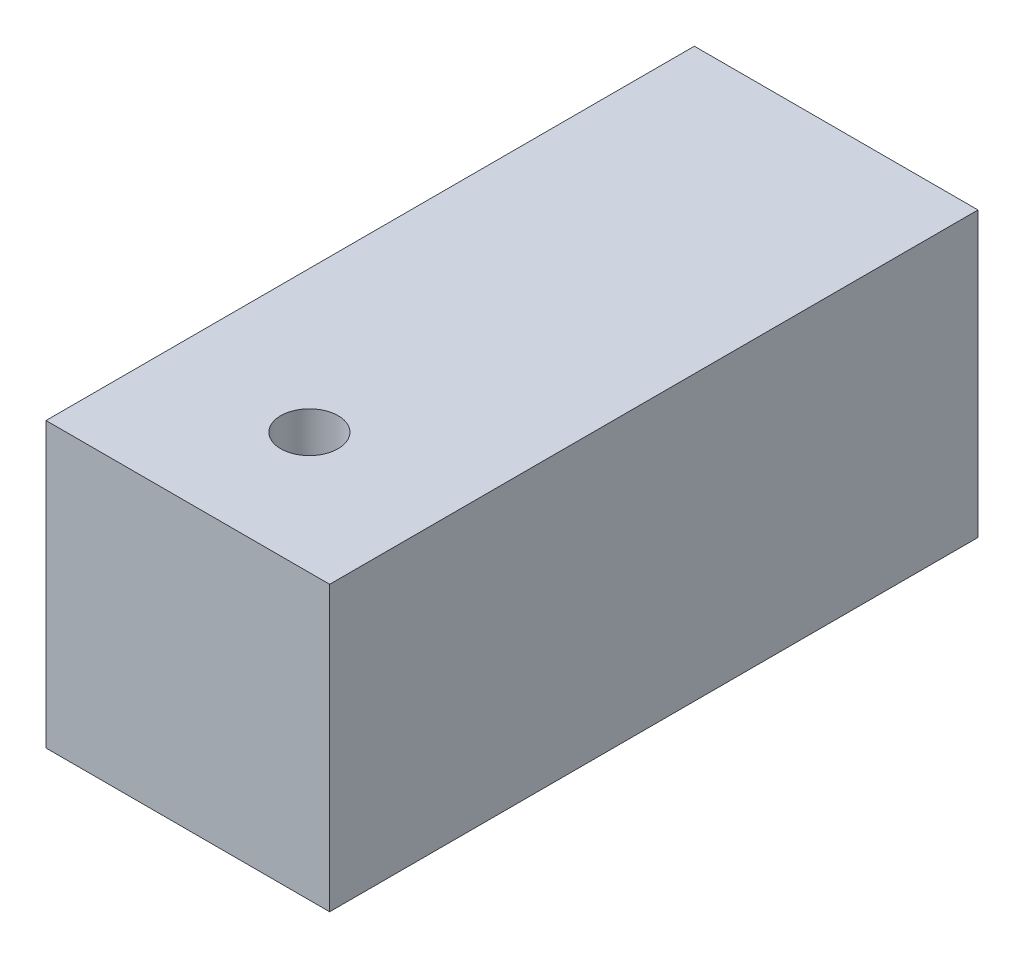
SolidWorks part; units mm, degrees
material "AISI 304"
ref_plane "Front Plane" through (0, 0, 0) normal (0, 0, 1) x (1, 0, 0)
ref_plane "Top Plane" through (0, 0, 0) normal (0, 1, 0) x (1, 0, 0)
ref_plane "Right Plane" through (0, 0, 0) normal (1, 0, 0) x (0, 0, -1)
sketch "Sketch1" plane through (0, 0, 0) normal (0, 0, 1) x (1, 0, 0)
  line L1 (-11.1125, 11.1125) -> (11.1125, 11.1125)
  line L2 (-11.1125, 11.1125) -> (-11.1125, -11.1125)
  line L3 (-11.1125, -11.1125) -> (11.1125, -11.1125)
  line L4 (11.1125, 11.1125) -> (11.1125, -11.1125)
  line L5 (-11.1125, 11.1125) -> (11.1125, -11.1125) construction
  line L6 (-11.1125, -11.1125) -> (11.1125, 11.1125) construction
  point P0 (0, 0)
  dimension "D1" = 22.225
  dimension "D2" = 22.225
extrude "Boss-Extrude1" add sketch "Sketch1" along normal blind 50.8
sketch "Sketch2" plane through (0, -11.1125, 0) normal (0, -1, 0) x (1, 0, 0)
  line L3 (-0.7938, 47.625) -> (0.7938, 47.625)
  line L4 (-3.9688, 44.45) -> (-3.9688, 38.1)
  line L5 (-0.7938, 34.925) -> (0.7938, 34.925)
  line L6 (3.9688, 44.45) -> (3.9688, 38.1)
  line L7 (-3.9688, 47.625) -> (3.9688, 34.925) construction
  line L8 (-3.9688, 34.925) -> (3.9688, 47.625) construction
  line L10 (-11.1125, 50.8) -> (11.1125, 50.8) construction
  circle A2 centre (0, 41.275) radius 6.35
  arc A3 (-3.9688, 38.1) -> (-0.7938, 34.925) centre (-0.7938, 38.1) ccw
  arc A4 (0.7938, 34.925) -> (3.9688, 38.1) centre (0.7938, 38.1) ccw
  arc A5 (3.9688, 44.45) -> (0.7938, 47.625) centre (0.7938, 44.45) ccw
  arc A6 (-0.7938, 47.625) -> (-3.9688, 44.45) centre (-0.7938, 44.45) ccw
  dimension "D2" = 12.7
  dimension "D1" = 3.175
  dimension "D3" = 7.9375
  dimension "D4" = 9.525
extrude "Cut-Extrude1" cut sketch "Sketch2" against normal blind 12.7 contours L4 A3 L5 A4 L6 A5 L3 A6
hole_wizard "#8 Clearance Hole1" positions "Sketch3" profile "Sketch4" hole size "#8" standard "ANSI Inch" end condition through all
sketch "Sketch3" plane through (0, 1.5875, 0) normal (0, -1, 0) x (-1, 0, 0)
  line L0 (-3.9688, -41.275) -> (3.9688, -41.275)
  line L1 (-3.9688, -44.45) -> (-3.9688, -38.1) construction
  line L2 (3.9688, -44.45) -> (3.9688, -38.1) construction
  point P0 (0, -41.275)
sketch "Sketch4" plane through (0, 1.5875, 41.275) normal (1, 0, 0) x (0, 0, -1)
  line L0 (0, 0) -> (0, 9.525)
  line L1 (0, 9.525) -> (2.2479, 9.525)
  line L2 (2.2479, 9.525) -> (2.2479, 0)
  line L5 (2.2479, 0) -> (0, 0)
  line L11 (0, -6.35) -> (0, 107.95) construction
  dimension "Thru Hole Dia." = 4.4958
  dimension "Thru Hole Depth" = 9.525
fillet "Fillet1" radius 0.381 8 edges at (-3.0388, -11.1125, 46.6951) (0, -11.1125, 47.625) (3.0388, -11.1125, 46.6951) (3.9688, -11.1125, 41.275) (3.0388, -11.1125, 35.8549) (0, -11.1125, 34.925) (-3.0388, -11.1125, 35.8549) (-3.9688, -11.1125, 41.275)
